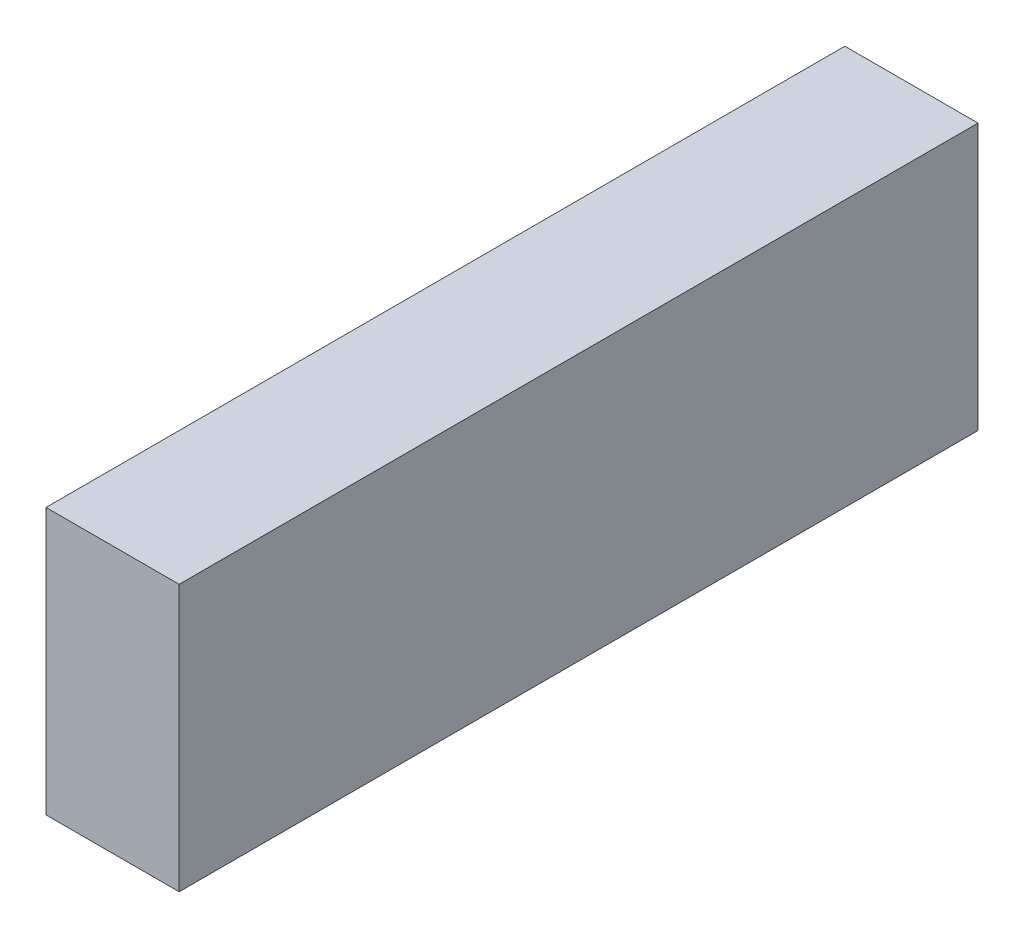
SolidWorks part; units mm, degrees
ref_plane "Front Plane" through (0, 0, 0) normal (0, 0, 1) x (1, 0, 0)
ref_plane "Top Plane" through (0, 0, 0) normal (0, 1, 0) x (1, 0, 0)
ref_plane "Right Plane" through (0, 0, 0) normal (1, 0, 0) x (0, 0, -1)
sketch "Sketch2" plane through (0, 0, 0) normal (1, 0, 0) x (0, 0, -1)
  line L3 (-262.7936, 0) -> (0, 0)
  line L4 (0, 0) -> (203.2, 0)
  line L6 (203.2, 0) -> (203.2, 81.9)
  line L7 (203.2, 81.9) -> (188.2, 81.9)
  line L8 (188.2, 81.9) -> (188.2, 20)
  line L9 (188.2, 20) -> (0, 20)
  line L10 (0, 20) -> (0, 133.7)
  line L11 (0, 133.7) -> (-115, 133.7)
  line L12 (-115, 133.7) -> (-171.1938, 94.3527)
  line L13 (-171.1938, 94.3527) -> (-262.7936, 81.4791)
  line L18 (-262.7936, 81.4791) -> (-262.7936, 31.4791)
  line L19 (-262.7936, 31.4791) -> (-262.7936, 0) construction
  arc A2 (-262.7936, 31.4791) -> (-262.7936, 0) centre (-255.1441, 15.7396) ccw
  dimension "D12" = 17.5
  dimension "D2" = 113.7
  dimension "D3" = 20
  dimension "D4" = 35
  dimension "D5" = 153
  dimension "D6" = 203.2
  dimension "D7" = 15
  dimension "D8" = 61.9
  dimension "D9" = 92.5
  dimension "D10" = 68.6
  dimension "D11" = 50
  dimension "D13" = 115
extrude "Boss-Extrude1" add sketch "Sketch2" along normal mid plane 138
sketch "Sketch4" plane through (0, 20, 0) normal (0, 1, 0) x (1, 0, 0)
  line L0 (69, 188.2) -> (-69, 188.2) construction
  line L1 (69, 0) -> (54, 0)
  line L2 (69, 0) -> (69, 188.2)
  line L3 (69, 188.2) -> (54, 188.2)
  line L4 (54, 0) -> (54, 188.2)
  dimension "D1" = 15
extrude "Boss-Extrude2" add sketch "Sketch4" along normal up to surface (61.9 mm away) up to face at (0, 81.9, -195.7)
mirror "Mirror1" about plane through (0, 0, 0) normal (1, 0, 0) of "Boss-Extrude2"
sketch "Sketch5" plane through (69, 0, 0) normal (1, 0, 0) x (0, 0, -1)
  line L0 (-262.7936, 0) -> (203.2, 0) construction
  line L1 (-224.9441, 0) -> (-160.3441, 0)
  line L2 (28.0559, 0) -> (92.6559, 0)
  arc A0 (-224.9441, 0) -> (-160.3441, 0) centre (-192.6441, 0) ccw
  arc A1 (28.0559, 0) -> (92.6559, 0) centre (60.3559, 0) ccw
  arc A2 (-262.7936, 31.4791) -> (-262.7936, 0) centre (-255.1441, 15.7396) ccw construction
  point P11 (-272.6441, 15.7396)
  dimension "D3" = 32.3
  dimension "D1" = 333
  dimension "D2" = 80
extrude "Boss-Extrude3" add sketch "Sketch5" against normal blind 20.4
mirror "Mirror2" about plane through (0, 0, 0) normal (1, 0, 0) of "Boss-Extrude3"
fillet "Fillet1" radius 10 5 edges at (0, 133.7, 0) (0, 133.7, 115) (0, 94.3527, 171.1938) (0, 81.4791, 262.7936) (0, 31.4791, 262.7936)
sketch "Sketch6" plane through (0, 0, 0) normal (1, 0, 0) x (0, 0, -1)
  line L0 (-192.6441, 0) -> (-192.6441, -32.3) construction
  line L1 (-2192.6441, -32.3) -> (3807.3559, -32.3)
  line L2 (-2192.6441, -32.3) -> (-2192.6441, 1967.7)
  line L3 (-2192.6441, 1967.7) -> (3807.3559, 1967.7)
  line L4 (3807.3559, -32.3) -> (3807.3559, 1967.7)
  arc A0 (-224.9441, 0) -> (-160.3441, 0) centre (-192.6441, 0) ccw construction
  dimension "D1" = 2000
  dimension "D2" = 6000
  dimension "D3" = 2000
extrude "Boss-Extrude4" add sketch "Sketch6" along normal blind 1000 separate body
sketch "Sketch8" plane through (0, 0, 0) normal (1, 0, 0) x (0, 0, -1)
  line L1 (-392.6441, -32.3) -> (487.3559, -32.3)
  line L2 (-392.6441, -32.3) -> (-392.6441, 407.7)
  line L3 (-392.6441, 407.7) -> (487.3559, 407.7)
  line L4 (487.3559, -32.3) -> (487.3559, 407.7)
  arc A0 (-224.9441, 0) -> (-160.3441, 0) centre (-192.6441, 0) ccw construction
  point P7 (-192.6441, -32.3)
  dimension "D1" = 880
  dimension "D2" = 440
  dimension "D3" = 200
extrude "Boss-Extrude5" add sketch "Sketch8" along normal blind 220 separate body
